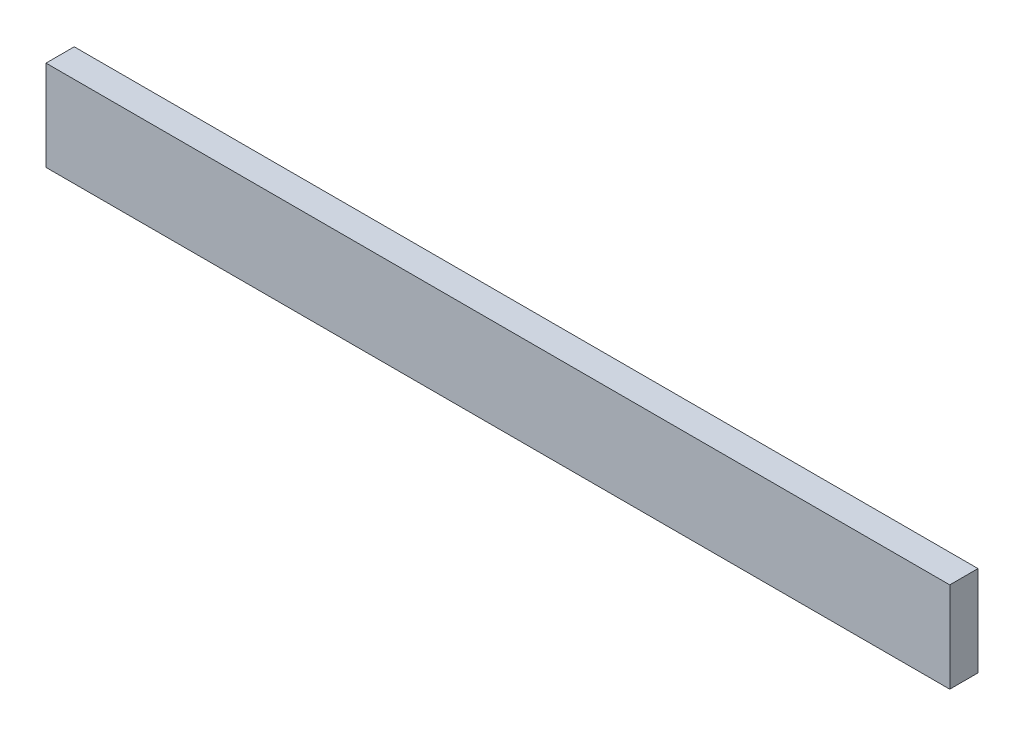
SolidWorks part; units mm, degrees
ref_plane "Front Plane" through (0, 0, 0) normal (0, 0, 1) x (1, 0, 0)
ref_plane "Top Plane" through (0, 0, 0) normal (0, 1, 0) x (1, 0, 0)
ref_plane "Right Plane" through (0, 0, 0) normal (1, 0, 0) x (0, 0, -1)
sketch "Sketch1" plane through (0, 0, 0) normal (0, 0, 1) x (1, 0, 0)
  line L1 (0, 0) -> (800, 0)
  line L2 (0, 0) -> (0, 80)
  line L3 (0, 80) -> (800, 80)
  line L4 (800, 0) -> (800, 80)
  dimension "D1" = 80
  dimension "D2" = 800
extrude "Boss-Extrude1" add sketch "Sketch1" along normal blind 25
